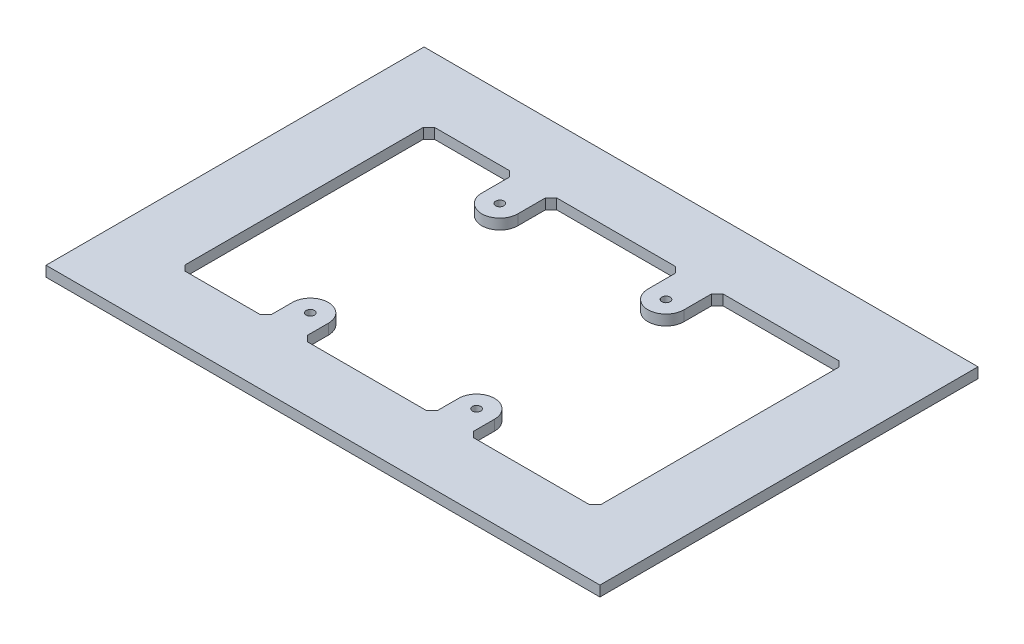
SolidWorks part; units mm, degrees
material "Delrin 2700 NC010, Low Viscosity Acetal Copolymer (SS)"
ref_plane "Front Plane" through (0, 0, 0) normal (0, 0, 1) x (1, 0, 0)
ref_plane "Top Plane" through (0, 0, 0) normal (0, 1, 0) x (1, 0, 0)
ref_plane "Right Plane" through (0, 0, 0) normal (1, 0, 0) x (0, 0, -1)
sketch "Sketch1" plane through (0, 0, 0) normal (0, 1, 0) x (1, 0, 0)
  line L1 (0, 0) -> (254, 0)
  line L2 (0, 0) -> (0, -173.355)
  line L3 (0, -173.355) -> (254, -173.355)
  line L4 (254, 0) -> (254, -173.355)
  dimension "D1" = 254
  dimension "D2" = 173.355
extrude "Boss-Extrude1" add sketch "Sketch1" along normal blind 4.7625
sketch "Sketch2" plane through (0, 4.7625, 0) normal (0, 1, 0) x (1, 0, 0)
  line L0 (0, -86.6775) -> (254, -86.6775) construction
  line L1 (0, 0) -> (0, -173.355) construction
  line L2 (254, -173.355) -> (254, 0) construction
  line L4 (222.25, -29.5275) -> (31.75, -29.5275)
  line L5 (222.25, -29.5275) -> (222.25, -143.8275)
  line L6 (222.25, -143.8275) -> (31.75, -143.8275)
  line L7 (31.75, -29.5275) -> (31.75, -143.8275)
  line L8 (222.25, -29.5275) -> (31.75, -143.8275) construction
  line L9 (222.25, -143.8275) -> (31.75, -29.5275) construction
  point P6 (127, -86.6775)
  dimension "D1" = 114.3
  dimension "D2" = 190.5
extrude "Cut-Extrude1" cut sketch "Sketch2" against normal blind 4.7625
sketch "Sketch3" plane through (0, 4.7625, 0) normal (0, 1, 0) x (1, 0, 0)
  line L0 (127, -29.5275) -> (127, -143.8275) construction
  line L1 (222.25, -29.5275) -> (31.75, -29.5275) construction
  line L2 (31.75, -143.8275) -> (222.25, -143.8275) construction
  line L3 (71.247, -44.7675) -> (71.247, -12.7)
  line L4 (219.71, -29.5275) -> (34.29, -29.5275) construction
  line L5 (219.71, -29.5275) -> (219.71, -143.8275) construction
  line L6 (219.71, -143.8275) -> (34.29, -143.8275) construction
  line L7 (34.29, -29.5275) -> (34.29, -143.8275) construction
  line L8 (219.71, -29.5275) -> (34.29, -143.8275) construction
  line L9 (219.71, -143.8275) -> (34.29, -29.5275) construction
  line L10 (155.702, -44.7675) -> (79.502, -44.7675) construction
  line L11 (155.702, -44.7675) -> (155.702, -131.6355) construction
  line L12 (155.702, -131.6355) -> (79.502, -131.6355) construction
  line L13 (79.502, -44.7675) -> (79.502, -131.6355) construction
  line L14 (155.702, -44.7675) -> (79.502, -131.6355) construction
  line L15 (71.247, -12.7) -> (87.757, -12.7)
  line L16 (87.757, -12.7) -> (87.757, -44.7675)
  line L17 (147.447, -44.7675) -> (147.447, -12.7)
  line L18 (147.447, -12.7) -> (163.957, -12.7)
  line L19 (163.957, -12.7) -> (163.957, -44.7675)
  line L21 (147.447, -163.703) -> (163.957, -163.703)
  line L22 (79.502, -88.2015) -> (155.702, -88.2015) construction
  line L23 (163.957, -163.703) -> (163.957, -131.6355)
  line L24 (147.447, -131.6355) -> (147.447, -163.703)
  line L25 (71.247, -163.703) -> (87.757, -163.703)
  line L26 (87.757, -163.703) -> (87.757, -131.6355)
  line L27 (71.247, -131.6355) -> (71.247, -163.703)
  arc A0 (71.247, -44.7675) -> (87.757, -44.7675) centre (79.502, -44.7675) ccw
  arc A1 (147.447, -44.7675) -> (163.957, -44.7675) centre (155.702, -44.7675) ccw
  arc A2 (147.447, -131.6355) -> (163.957, -131.6355) centre (155.702, -131.6355) cw
  arc A3 (71.247, -131.6355) -> (87.757, -131.6355) centre (79.502, -131.6355) cw
  point P6 (127, -86.6775)
  point P11 (127, -86.6775)
  line M2 (31.75, -29.5275) -> (222.25, -29.5275)
  line M4 (222.25, -143.8275) -> (31.75, -143.8275)
  dimension "D7" = 8.255
  dimension "D9" = 8.255
  dimension "D1" = 185.42
  dimension "D2" = 114.3
  dimension "D3" = 45.212
  dimension "D4" = 15.24
  dimension "D5" = 76.2
  dimension "D6" = 86.868
  dimension "D8" = 12.7
  dimension "D10" = 59.69
extrude "Boss-Extrude2" add sketch "Sketch3" against normal blind 4.7625 contours L17 A1 L19 M2 | L3 A0 L16 M2 | A3 L27 L26 M4 | A2 L24 L23 M4
hole_wizard "#6 Clearance Hole1" positions "Sketch5" profile "Sketch6" hole size "#6" standard "Ansi Inch"
sketch "Sketch5" plane through (0, 4.7625, 0) normal (0, 1, 0) x (-1, 0, 0)
  line L0 (-71.247, 44.7675) -> (-87.757, 44.7675) construction
  line L2 (-147.447, 44.7675) -> (-163.957, 44.7675) construction
  line L4 (-71.247, 131.6355) -> (-87.757, 131.6355) construction
  line L6 (-147.447, 131.6355) -> (-163.957, 131.6355) construction
  point P0 (-79.502, 44.7675)
  point P1 (-155.702, 44.7675)
  point P3 (-79.502, 131.6355)
  point P5 (-155.702, 131.6355)
sketch "Sketch6" plane through (79.502, 4.7625, 44.7675) normal (1, 0, 0) x (0, 0, 1)
  line L0 (0, 0) -> (0, 26.5408)
  line L1 (0, 26.5408) -> (1.8986, 25.4)
  line L2 (1.8986, 25.4) -> (1.8986, 0)
  line L5 (1.8986, 0) -> (0, 0)
  line L10 (0, 26.5408) -> (-1.8987, 25.4) construction
  line L11 (0, -6.35) -> (0, 107.95) construction
  dimension "Hole Dia." = 3.7973
  dimension "Hole Depth" = 25.4
  dimension "Drill Angle" = 118
chamfer "Chamfer1" distance 2.54 angle 45 12 edges at (87.757, 2.3813, 143.8275) (71.247, 2.3813, 143.8275) (147.447, 2.3813, 143.8275) (163.957, 2.3813, 143.8275) (222.25, 2.3813, 143.8275) (222.25, 2.3813, 29.5275) (163.957, 2.3813, 29.5275) (147.447, 2.3813, 29.5275) (71.247, 2.3813, 29.5275) (87.757, 2.3813, 29.5275) (31.75, 2.3813, 29.5275) (31.75, 2.3813, 143.8275)
